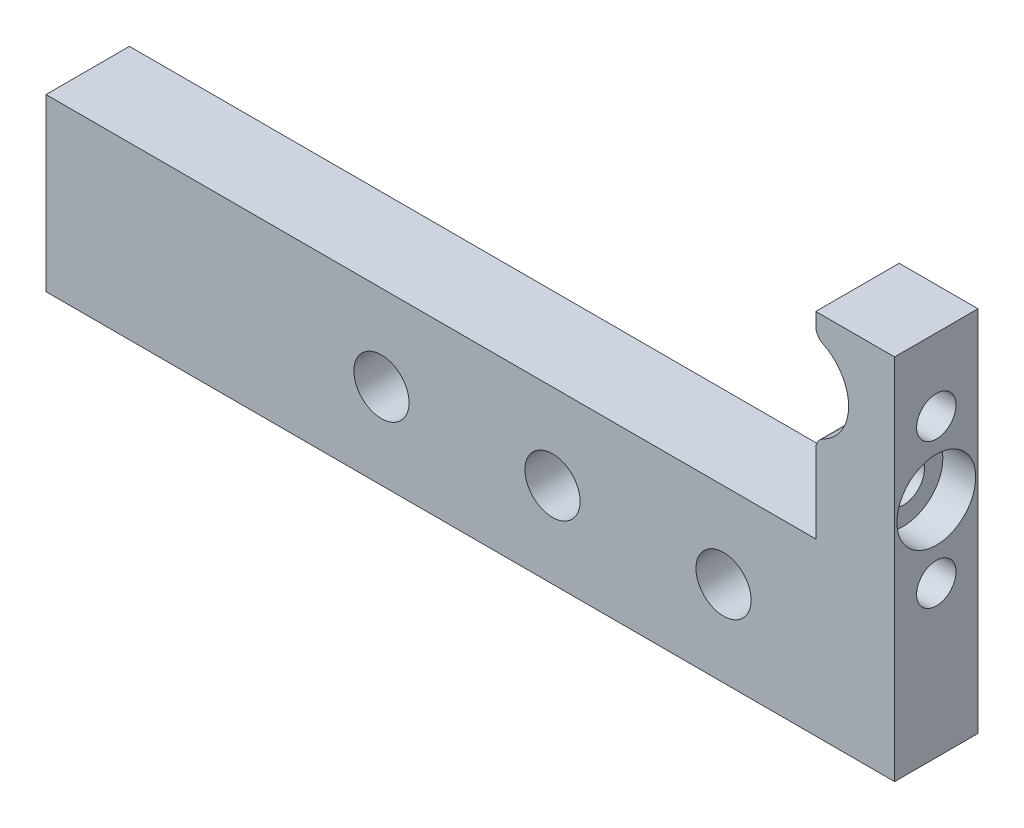
SolidWorks part; units mm, degrees
material "Plain Carbon Steel"
ref_plane "Front Plane" through (0, 0, 0) normal (0, 0, 1) x (1, 0, 0)
ref_plane "Top Plane" through (0, 0, 0) normal (0, 1, 0) x (1, 0, 0)
ref_plane "Right Plane" through (0, 0, 0) normal (1, 0, 0) x (0, 0, -1)
sketch "Sketch1" plane through (0, 0, 0) normal (0, 0, 1) x (1, 0, 0)
  line L0 (45.4, -16) -> (45.4, -29) construction
  line L1 (40.4, -16) -> (99, -16) construction
  line L2 (104, -16) -> (99, -16) construction
  line L3 (104, -1) -> (104, -16) construction
  line L4 (104, -1) -> (110, -1) construction
  line L5 (110, -29) -> (110, -1) construction
  line L6 (45.4, -29) -> (110, -29) construction
  line L7 (45.4, -16) -> (45.4, -29)
  line L8 (45.4, -16) -> (99, -16)
  line L9 (104, -16) -> (99, -16)
  line L10 (104, -1) -> (104, -2.6459)
  line L11 (104, -1) -> (110, -1)
  line L12 (110, -29) -> (110, -1)
  line L13 (45.4, -29) -> (110, -29)
  line L14 (104, -9.3541) -> (104, -16)
  circle A0 centre (103, -6) radius 3.5 construction
  arc A1 (104, -9.3541) -> (104, -2.6459) centre (103, -6) ccw
  circle A2 centre (96.9786, -22.5) radius 2.1 construction
  circle A3 centre (83.9573, -22.5) radius 2.1 construction
  circle A4 centre (70.9359, -22.5) radius 2.1 construction
  circle A5 centre (96.9786, -22.5) radius 2.1
  circle A6 centre (83.9573, -22.5) radius 2.1
  circle A7 centre (70.9359, -22.5) radius 2.1
extrude "Boss-Extrude1" add sketch "Sketch1" along normal blind 6.35
sketch "Sketch2" plane through (110, 0, 0) normal (1, 0, 0) x (0, 0, -1)
  line L0 (-3.175, -17.5) -> (-3.175, -6.5) construction
  circle A0 centre (-3.175, -12) radius 1.6
  circle A1 centre (-3.175, -6.5) radius 1.5 construction
  circle A2 centre (-3.175, -17.5) radius 1.5 construction
  dimension "D1" = 3.2
  dimension "D3" = 3
  dimension "D2" = 11
extrude "Cut-Extrude1" cut sketch "Sketch2" against normal through all
sketch "Sketch3" plane through (110, 0, 0) normal (1, 0, 0) x (0, 0, -1)
  circle A0 centre (-3.175, -12) radius 3
  dimension "D1" = 6
extrude "Cut-Extrude2" cut sketch "Sketch3" against normal blind 2.5
sketch "Sketch4" plane through (110, 0, 0) normal (1, 0, 0) x (0, 0, -1)
  circle A0 centre (-3.175, -17.5) radius 1.5 construction
  circle A1 centre (-3.175, -6.5) radius 1.5 construction
  circle A2 centre (-3.175, -17.5) radius 1.5
  circle A3 centre (-3.175, -6.5) radius 1.5
extrude "Cut-Extrude3" cut sketch "Sketch4" against normal blind 5
fillet "Fillet1" radius 1 2 edges at (104, -2.6459, 3.175) (104, -9.3541, 3.175)
